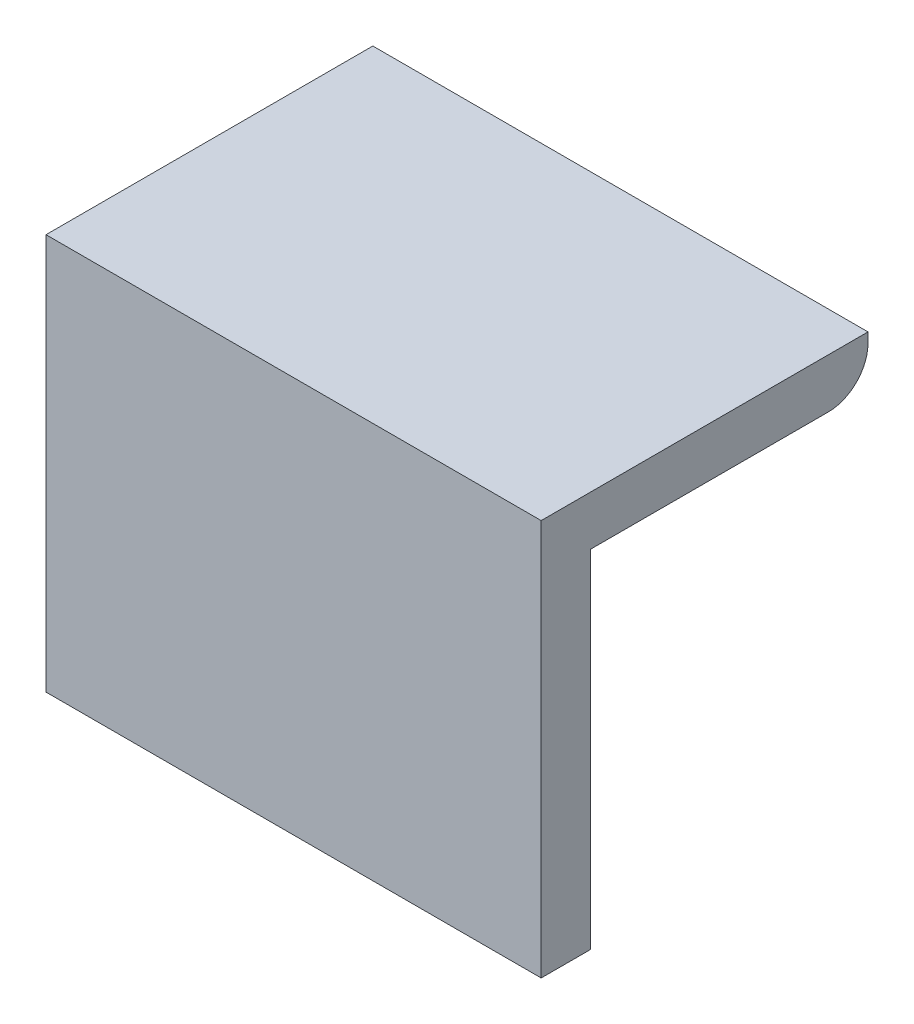
SolidWorks part; units mm, degrees
material "Pine"
ref_plane "Front Plane" through (0, 0, 0) normal (0, 0, 1) x (1, 0, 0)
ref_plane "Top Plane" through (0, 0, 0) normal (0, 1, 0) x (1, 0, 0)
ref_plane "Right Plane" through (0, 0, 0) normal (1, 0, 0) x (0, 0, -1)
sketch "Sketch1" plane through (0, 0, 0) normal (0, 0, 1) x (1, 0, 0)
  line L1 (-25, -20) -> (25, -20)
  line L2 (-25, -20) -> (-25, 20)
  line L3 (-25, 20) -> (25, 20)
  line L4 (25, -20) -> (25, 20)
  line L5 (-25, -20) -> (25, 20) construction
  line L6 (-25, 20) -> (25, -20) construction
  point P0 (0, 0)
  dimension "D1" = 40
  dimension "D2" = 50
extrude "Boss-Extrude1" add sketch "Sketch1" along normal blind 5
sketch "Sketch2" plane through (0, 0, 0) normal (0, 0, -1) x (-1, 0, 0)
  line L0 (25, 20) -> (25, -20) construction
  line L1 (-25, 15) -> (25, 15)
  line L2 (-25, 15) -> (-25, 20)
  line L3 (-25, 20) -> (25, 20)
  line L4 (25, 15) -> (25, 20)
  line L5 (-25, 15) -> (25, 20) construction
  line L6 (-25, 20) -> (25, 15) construction
  line L7 (-25, 20) -> (25, 20) construction
  point P0 (0, 17.5)
  dimension "D1" = 50
  dimension "D2" = 5
  dimension "D3" = 2.5
extrude "Boss-Extrude2" add sketch "Sketch2" along normal blind 28
fillet "Fillet1" radius 4 1 edges at (0, 15, -28)
